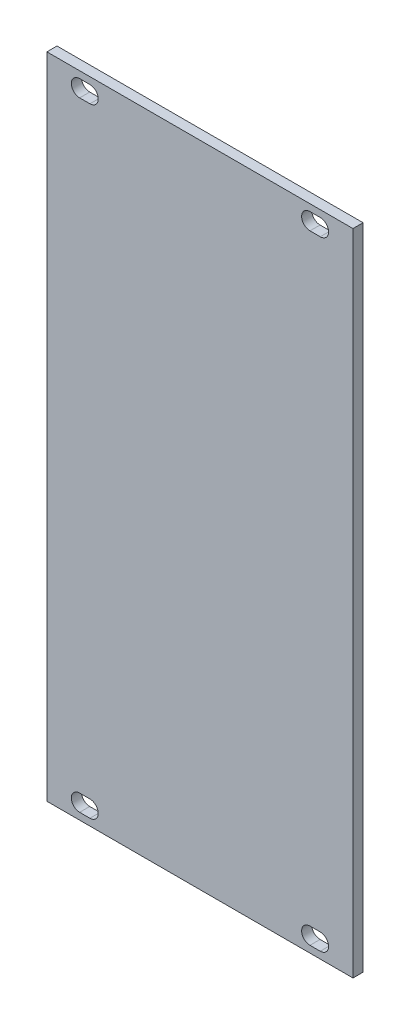
SolidWorks part; units mm, degrees
ref_plane "Front Plane" through (0, 0, 0) normal (0, 0, 1) x (1, 0, 0)
ref_plane "Top Plane" through (0, 0, 0) normal (0, 1, 0) x (1, 0, 0)
ref_plane "Right Plane" through (0, 0, 0) normal (1, 0, 0) x (0, 0, -1)
sketch "Sketch1" plane through (0, 0, 0) normal (0, 0, 1) x (1, 0, 0)
  line L0 (-22.8, 64.25) -> (-22.8, -64.25) construction
  line L1 (-30.3, 64.25) -> (30.3, 64.25)
  line L2 (-30.3, 64.25) -> (-30.3, -64.25)
  line L3 (-30.3, -64.25) -> (30.3, -64.25)
  line L4 (30.3, 64.25) -> (30.3, -64.25)
  line L5 (-30.3, 64.25) -> (30.3, -64.25) construction
  line L6 (-30.3, -64.25) -> (30.3, 64.25) construction
  line L7 (-30.3, 61.25) -> (30.3, 61.25) construction
  line L8 (-30.3, -61.25) -> (30.3, -61.25) construction
  line L9 (-23.816, -61.25) -> (-21.784, -61.25) construction
  line L10 (21.784, 61.25) -> (23.816, 61.25) construction
  line L11 (-23.816, -59.6) -> (-21.784, -59.6)
  line L12 (-23.816, -62.9) -> (-21.784, -62.9)
  line L13 (-23.816, 61.25) -> (-21.784, 61.25) construction
  line L14 (-23.816, 62.9) -> (-21.784, 62.9)
  line L15 (-23.816, 59.6) -> (-21.784, 59.6)
  line L16 (21.784, 62.9) -> (23.816, 62.9)
  line L17 (21.784, 59.6) -> (23.816, 59.6)
  line L18 (21.784, -61.25) -> (23.816, -61.25) construction
  line L19 (21.784, -59.6) -> (23.816, -59.6)
  line L20 (21.784, -62.9) -> (23.816, -62.9)
  line L21 (22.8, 64.25) -> (22.8, -64.25) construction
  arc A0 (-23.816, -59.6) -> (-23.816, -62.9) centre (-23.816, -61.25) ccw
  arc A1 (-21.784, -62.9) -> (-21.784, -59.6) centre (-21.784, -61.25) ccw
  arc A2 (-23.816, 62.9) -> (-23.816, 59.6) centre (-23.816, 61.25) ccw
  arc A3 (-21.784, 59.6) -> (-21.784, 62.9) centre (-21.784, 61.25) ccw
  arc A4 (21.784, 62.9) -> (21.784, 59.6) centre (21.784, 61.25) ccw
  arc A5 (23.816, 59.6) -> (23.816, 62.9) centre (23.816, 61.25) ccw
  arc A6 (21.784, -59.6) -> (21.784, -62.9) centre (21.784, -61.25) ccw
  arc A7 (23.816, -62.9) -> (23.816, -59.6) centre (23.816, -61.25) ccw
  point P0 (0, 0)
  point P8 (22.8, 61.25)
  point P18 (-22.8, -61.25)
  point P24 (-22.8, 61.25)
  point P34 (22.8, -61.25)
  point P42 (0, 0)
  point P43 (0, 0)
  dimension "D6" = 1.65
  dimension "D7" = 1.65
  dimension "D11" = 1.65
  dimension "D13" = 1.65
  dimension "D1" = 128.5
  dimension "D2" = 60.6
  dimension "D3" = 7.5
  dimension "D4" = 3
  dimension "D8" = 2.032
  dimension "D9" = 2.032
  dimension "D10" = 7.5
  dimension "D12" = 2.032
  dimension "D14" = 2.032
  dimension "D5" = 3
extrude "Boss-Extrude1" add sketch "Sketch1" along normal blind 2
